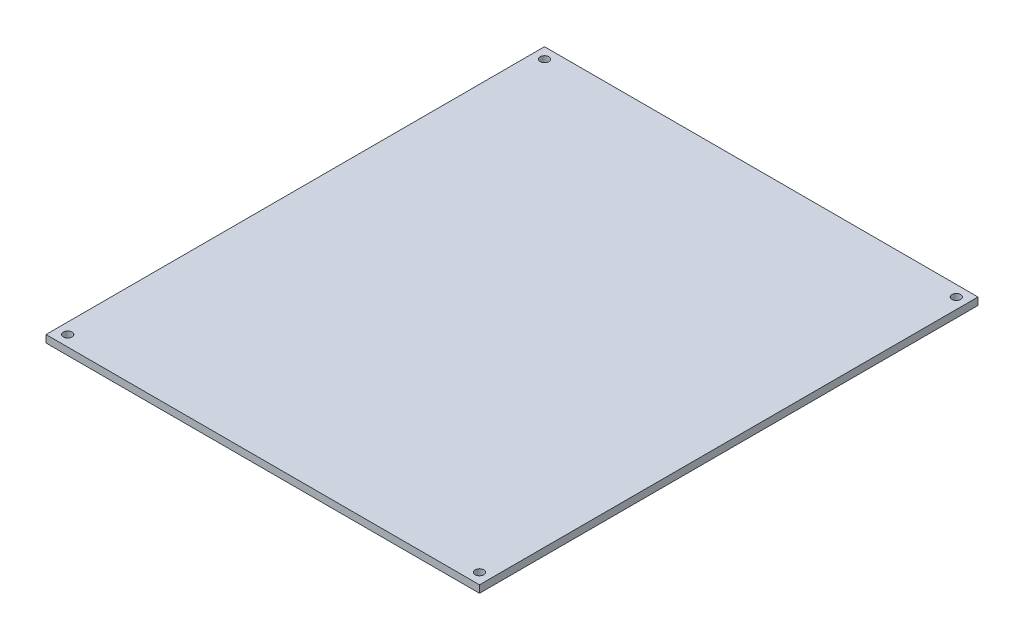
SolidWorks part; units mm, degrees
ref_plane "Front Plane" through (0, 0, 0) normal (0, 0, 1) x (1, 0, 0)
ref_plane "Top Plane" through (0, 0, 0) normal (0, 1, 0) x (1, 0, 0)
ref_plane "Right Plane" through (0, 0, 0) normal (1, 0, 0) x (0, 0, -1)
sketch "Sketch1" plane through (0, 0, 0) normal (0, 1, 0) x (1, 0, 0)
  line L1 (-50, -57.5) -> (50, -57.5)
  line L2 (-50, -57.5) -> (-50, 57.5)
  line L3 (-50, 57.5) -> (50, 57.5)
  line L4 (50, -57.5) -> (50, 57.5)
  line L5 (-50, -57.5) -> (50, 57.5) construction
  line L6 (-50, 57.5) -> (50, -57.5) construction
  point P0 (0, 0)
  dimension "D1" = 115
  dimension "D2" = 100
extrude "Boss-Extrude1" add sketch "Sketch1" along normal blind 1.7
sketch "Sketch2" plane through (0, 0, 0) normal (0, -1, 0) x (1, 0, 0)
  line L0 (50, 57.5) -> (50, -57.5) construction
  line L1 (-50, 57.5) -> (50, 57.5) construction
  line L2 (50, -57.5) -> (-50, -57.5) construction
  line L3 (-50, -57.5) -> (-50, 57.5) construction
  circle A0 centre (47.5, 55) radius 1
  circle A1 centre (-47.5, 55) radius 1
  circle A2 centre (-47.5, -55) radius 1
  circle A3 centre (47.5, -55) radius 1
  dimension "D3" = 2
  dimension "D6" = 2
  dimension "D7" = 2
  dimension "D8" = 2
  dimension "D1" = 2.5
  dimension "D2" = 2.5
  dimension "D4" = 2.5
  dimension "D5" = 2.5
extrude "Cut-Extrude1" cut sketch "Sketch2" against normal blind 21.7
